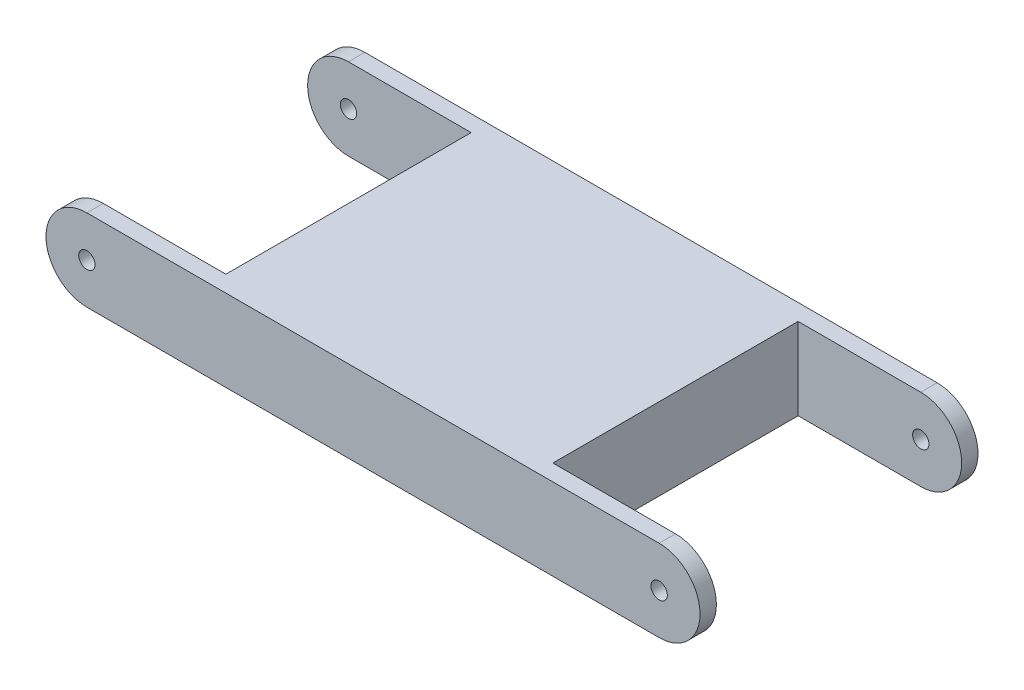
SolidWorks part; units mm, degrees
ref_plane "前基準面" through (0, 0, 0) normal (0, 0, 1) x (1, 0, 0)
ref_plane "上基準面" through (0, 0, 0) normal (0, 1, 0) x (1, 0, 0)
ref_plane "右基準面" through (0, 0, 0) normal (1, 0, 0) x (0, 0, -1)
sketch "草圖1" plane through (0, 0, 0) normal (0, 0, 1) x (1, 0, 0)
  line L0 (0, 47.1991) -> (0, -46.8309) construction
  line L1 (-71.1827, 0) -> (68.2665, 0) construction
  line L2 (-35, 0) -> (35, 0) construction
  line L3 (-35, 5) -> (35, 5)
  line L4 (-35, -5) -> (35, -5)
  arc A0 (-35, 5) -> (-35, -5) centre (-35, 0) ccw
  arc A1 (35, -5) -> (35, 5) centre (35, 0) ccw
  point P7 (0, 0)
  point P12 (0, 0)
  dimension "D2" = 5
  dimension "D1" = 70
extrude "填料-伸長1" add sketch "草圖1" along normal blind 34
sketch "草圖2" plane through (0, 0, 0) normal (0, 0, 1) x (1, 0, 0)
  line L0 (-45.1846, 0) -> (43.8227, 0) construction
  line L1 (0, 28.0802) -> (0, -27.5995) construction
  circle A0 centre (-35, 0) radius 1
  circle A1 centre (35, 0) radius 1
  dimension "D1" = 2
extrude "除料-伸長4" cut sketch "草圖2" against normal blind 30 and the other way through all
sketch "草圖3" plane through (0, 0, 0) normal (0, 1, 0) x (1, 0, 0)
  line L0 (35, 0) -> (-35, 0) construction
  line L1 (-40, -2) -> (-20, -2)
  line L2 (-40, -2) -> (-40, -32)
  line L3 (-40, -32) -> (-20, -32)
  line L4 (-20, -2) -> (-20, -32)
  line L5 (-35, -34) -> (-35, 0) construction
  line L6 (0, 16.8532) -> (0, -37.2241) construction
  line L7 (20, -2) -> (20, -32)
  line L8 (40, -32) -> (20, -32)
  line L9 (40, -2) -> (40, -32)
  line L10 (40, -2) -> (20, -2)
  dimension "D1" = 20
  dimension "D2" = 30
  dimension "D3" = 2
  dimension "D4" = 15
extrude "除料-伸長5" cut sketch "草圖3" against normal blind 30 and the other way blind 30
